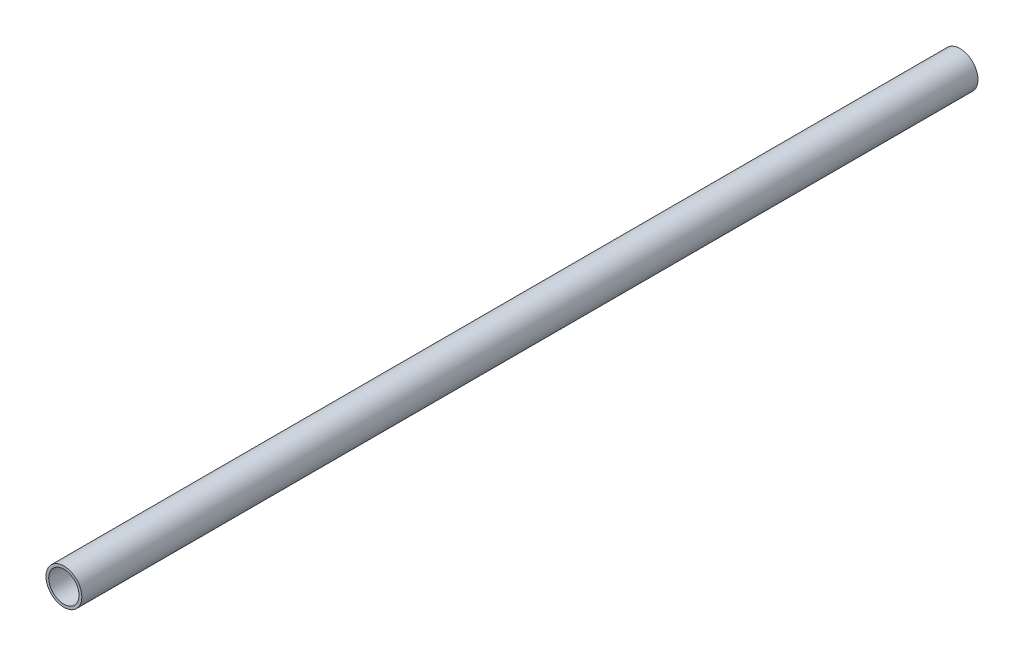
SolidWorks part; units mm, degrees
ref_plane "Alzado" through (0, 0, 0) normal (0, 0, 1) x (1, 0, 0)
ref_plane "Planta" through (0, 0, 0) normal (0, 1, 0) x (1, 0, 0)
ref_plane "Vista lateral" through (0, 0, 0) normal (1, 0, 0) x (0, 0, -1)
sketch "Croquis1" plane through (0, 0, 0) normal (0, 0, 1) x (1, 0, 0)
  circle A0 centre (0, 0) radius 30
  point P3 (0, 0)
  dimension "D1" = 60
extrude "Saliente-Extruir1" add sketch "Croquis1" along normal blind 1500
ref_plane "Plano1" through (0, 0, 1500) normal (0, 0, 1) x (1, 0, 0)
sketch "Croquis2" plane through (0, 0, 1500) normal (0, 0, 1) x (1, 0, 0)
  circle A0 centre (0, 0) radius 25.4
  circle A1 centre (0, 0) radius 30 construction
  dimension "D1" = 4.6
extrude "Cortar-Extruir1" cut sketch "Croquis2" against normal through all
